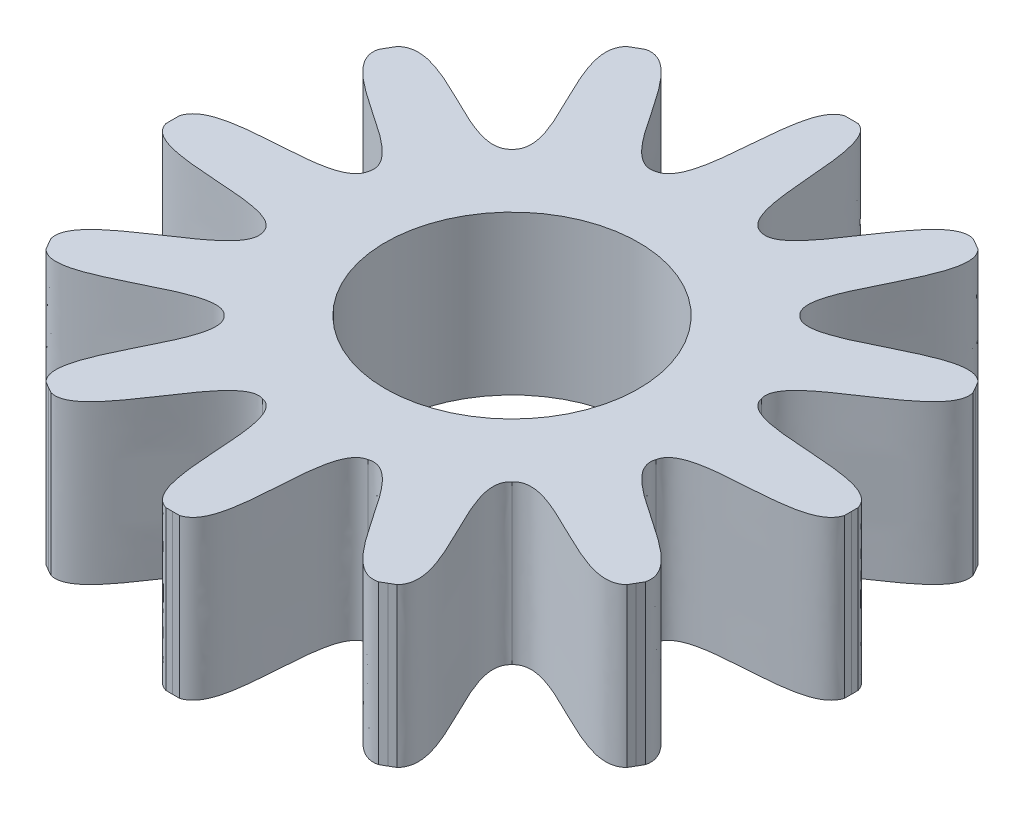
SolidWorks part; units mm, degrees
ref_plane "Alzado" through (0, 0, 0) normal (0, 0, 1) x (1, 0, 0)
ref_plane "Planta" through (0, 0, 0) normal (0, 1, 0) x (1, 0, 0)
ref_plane "Vista lateral" through (0, 0, 0) normal (1, 0, 0) x (0, 0, -1)
sketch "Sketch1" plane through (0, 0, 0) normal (0, 1, 0) x (1, 0, 0)
  line L0 (0, -1000) -> (0, 49000) construction
  line L1 (0, 0) -> (12940.9523, 48296.2913) construction
  line L2 (0, 0.75) -> (0.015, 0.7499)
  line L3 (0, 0.75) -> (-0.015, 0.7499)
  line L4 (0.375, 0.6495) -> (0.3619, 0.6569)
  line L5 (0.375, 0.6495) -> (0.3879, 0.6419)
  line L6 (0.6495, 0.375) -> (0.6419, 0.3879)
  line L7 (0.6495, 0.375) -> (0.6569, 0.3619)
  line L8 (0.75, 0) -> (0.7499, 0.015)
  line L9 (0.75, 0) -> (0.7499, -0.015)
  line L10 (0.6495, -0.375) -> (0.6569, -0.3619)
  line L11 (0.6495, -0.375) -> (0.6419, -0.3879)
  line L12 (0.375, -0.6495) -> (0.3879, -0.6419)
  line L13 (0.375, -0.6495) -> (0.3619, -0.6569)
  line L14 (0, -0.75) -> (0.015, -0.7499)
  line L15 (0, -0.75) -> (-0.015, -0.7499)
  line L16 (-0.375, -0.6495) -> (-0.3619, -0.6569)
  line L17 (-0.375, -0.6495) -> (-0.3879, -0.6419)
  line L18 (-0.6495, -0.375) -> (-0.6419, -0.3879)
  line L19 (-0.6495, -0.375) -> (-0.6569, -0.3619)
  line L20 (-0.75, 0) -> (-0.7499, -0.015)
  line L21 (-0.75, 0) -> (-0.7498, 0.015)
  line L22 (-0.6495, 0.375) -> (-0.6569, 0.3619)
  line L23 (-0.6495, 0.375) -> (-0.6419, 0.3879)
  line L24 (-0.375, 0.6495) -> (-0.3879, 0.6419)
  line L25 (-0.375, 0.6495) -> (-0.3619, 0.6569)
  circle A0 centre (0, 0) radius 0.75 construction
  circle A1 centre (0, 0) radius 0.45 construction
  spline S0 degree 3 poles (0.015, 0.7499) (0.0898, 0.7265) (0.0375, 0.4506) (0.1165, 0.4347) knots 0 0 0 0 1 1 1 1
  spline S1 degree 3 poles (-0.015, 0.7499) (-0.0898, 0.7265) (-0.0375, 0.4506) (-0.1165, 0.4347) knots 0 0 0 0 1 1 1 1
  spline S2 degree 3 poles (0.3619, 0.6569) (0.2767, 0.6794) (0.1928, 0.409) (0.1165, 0.4347) knots 0 0 0 0 1 1 1 1
  spline S3 degree 3 poles (0.3879, 0.6419) (0.4501, 0.5793) (0.2578, 0.3714) (0.3182, 0.3182) knots 0 0 0 0 1 1 1 1
  spline S4 degree 3 poles (0.6419, 0.3879) (0.5793, 0.4501) (0.3714, 0.2578) (0.3182, 0.3182) knots 0 0 0 0 1 1 1 1
  spline S5 degree 3 poles (0.6569, 0.3619) (0.6794, 0.2767) (0.409, 0.1928) (0.4347, 0.1165) knots 0 0 0 0 1 1 1 1
  spline S6 degree 3 poles (0.7499, 0.015) (0.7268, 0.1001) (0.4506, 0.0375) (0.4347, 0.1165) knots 0 0 0 0 1 1 1 1
  spline S7 degree 3 poles (0.7499, -0.015) (0.7268, -0.1001) (0.4506, -0.0375) (0.4347, -0.1165) knots 0 0 0 0 1 1 1 1
  spline S8 degree 3 poles (0.6569, -0.3619) (0.6794, -0.2767) (0.409, -0.1928) (0.4347, -0.1165) knots 0 0 0 0 1 1 1 1
  spline S9 degree 3 poles (0.6419, -0.3879) (0.5793, -0.4501) (0.3714, -0.2578) (0.3182, -0.3182) knots 0 0 0 0 1 1 1 1
  spline S10 degree 3 poles (0.3879, -0.6419) (0.4501, -0.5793) (0.2578, -0.3714) (0.3182, -0.3182) knots 0 0 0 0 1 1 1 1
  spline S11 degree 3 poles (0.3619, -0.6569) (0.2767, -0.6794) (0.1928, -0.409) (0.1165, -0.4347) knots 0 0 0 0 1 1 1 1
  spline S12 degree 3 poles (0.015, -0.7498) (0.1001, -0.7268) (0.0375, -0.4506) (0.1165, -0.4347) knots 0 0 0 0 1 1 1 1
  spline S13 degree 3 poles (-0.015, -0.7498) (-0.1001, -0.7268) (-0.0375, -0.4506) (-0.1165, -0.4347) knots 0 0 0 0 1 1 1 1
  spline S14 degree 3 poles (-0.3619, -0.6569) (-0.2767, -0.6794) (-0.1928, -0.409) (-0.1165, -0.4347) knots 0 0 0 0 1 1 1 1
  spline S15 degree 3 poles (-0.3879, -0.6419) (-0.4501, -0.5793) (-0.2578, -0.3714) (-0.3182, -0.3182) knots 0 0 0 0 1 1 1 1
  spline S16 degree 3 poles (-0.6419, -0.3879) (-0.5793, -0.4501) (-0.3714, -0.2578) (-0.3182, -0.3182) knots 0 0 0 0 1 1 1 1
  spline S17 degree 3 poles (-0.6569, -0.3619) (-0.6794, -0.2767) (-0.409, -0.1928) (-0.4347, -0.1165) knots 0 0 0 0 1 1 1 1
  spline S18 degree 3 poles (-0.7498, -0.015) (-0.7268, -0.1001) (-0.4506, -0.0375) (-0.4347, -0.1165) knots 0 0 0 0 1 1 1 1
  spline S19 degree 3 poles (-0.7498, 0.015) (-0.7268, 0.1001) (-0.4506, 0.0375) (-0.4347, 0.1165) knots 0 0 0 0 1 1 1 1
  spline S20 degree 3 poles (-0.6569, 0.3619) (-0.6794, 0.2767) (-0.409, 0.1928) (-0.4347, 0.1165) knots 0 0 0 0 1 1 1 1
  spline S21 degree 3 poles (-0.6419, 0.3879) (-0.5793, 0.4501) (-0.3714, 0.2578) (-0.3182, 0.3182) knots 0 0 0 0 1 1 1 1
  spline S22 degree 3 poles (-0.3879, 0.6419) (-0.4501, 0.5793) (-0.2578, 0.3714) (-0.3182, 0.3182) knots 0 0 0 0 1 1 1 1
  spline S23 degree 3 poles (-0.3619, 0.6569) (-0.2767, 0.6794) (-0.1928, 0.409) (-0.1165, 0.4347) knots 0 0 0 0 1 1 1 1
  point P4 (0.015, 0.7499)
  point P9 (0, 0.75)
  point P10 (0.1165, 0.4347)
  point P74 (0, 0)
  dimension "D1" = 1.5
  dimension "D2" = 0.9
  dimension "D3" = 15
  dimension "D4" = 0.015
  dimension "D5" = 12
extrude "Boss-Extrude1" add sketch "Sketch1" along normal blind 0.35
sketch "Sketch2" plane through (0, 0, 0) normal (0, 1, 0) x (1, 0, 0)
  circle A0 centre (0, 0) radius 0.28
  dimension "D1" = 0.56
extrude "Cut-Extrude1" cut sketch "Sketch2" along normal through all
